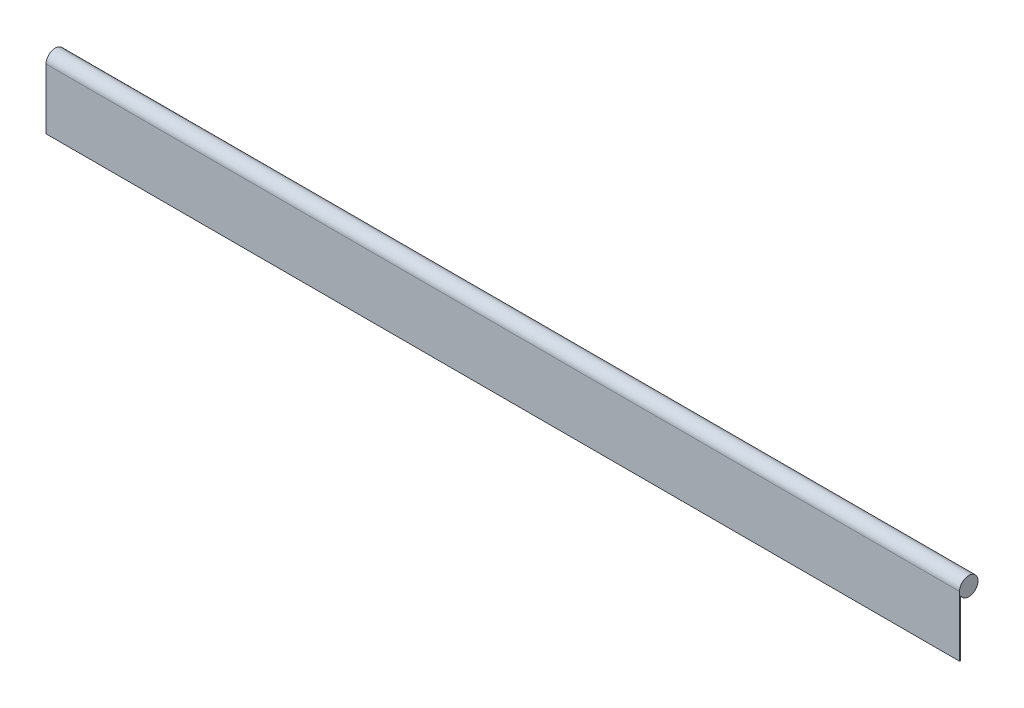
SolidWorks part; units mm, degrees
ref_plane "Front Plane" through (0, 0, 0) normal (0, 0, 1) x (1, 0, 0)
ref_plane "Top Plane" through (0, 0, 0) normal (0, 1, 0) x (1, 0, 0)
ref_plane "Right Plane" through (0, 0, 0) normal (1, 0, 0) x (0, 0, -1)
sketch "Sketch1" plane through (0, 0, 0) normal (1, 0, 0) x (0, 0, -1)
  line L0 (-17.4625, 0) -> (-17.4625, -114.3)
  line L1 (-17.4625, -114.3) -> (-15.875, -114.3)
  line L2 (-15.875, -114.3) -> (-15.875, -7.2748)
  arc A0 (-15.875, -7.2748) -> (-17.4625, 0) centre (0, 0) ccw
  dimension "D1" = 17.4625
  dimension "D2" = 1.5875
  dimension "D3" = 114.3
extrude "Boss-Extrude1" add sketch "Sketch1" along normal blind 1727.2
